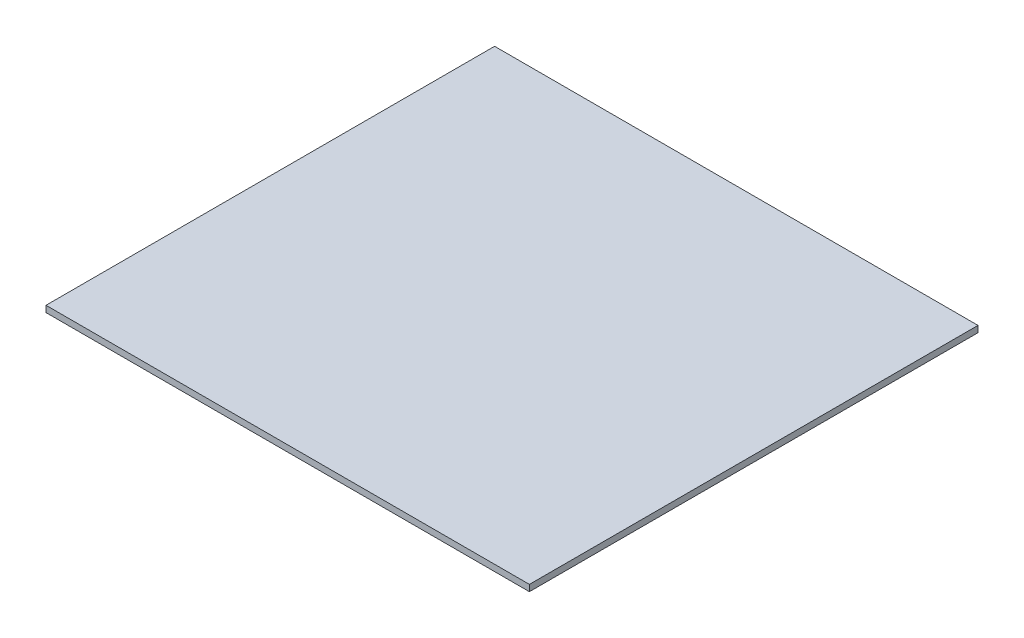
SolidWorks part; units mm, degrees
ref_plane "Front Plane" through (0, 0, 0) normal (0, 0, 1) x (1, 0, 0)
ref_plane "Top Plane" through (0, 0, 0) normal (0, 1, 0) x (1, 0, 0)
ref_plane "Right Plane" through (0, 0, 0) normal (1, 0, 0) x (0, 0, -1)
sketch "Sketch2" plane through (0, 0, 0) normal (0, 0, 1) x (1, 0, 0)
  line L0 (0, 25) -> (-380, 25)
  line L1 (-380, 25) -> (-380, 15)
  line L2 (-380, 15) -> (-225, 15)
  line L3 (-225, 15) -> (-225, 0)
  line L4 (-225, 0) -> (0, 0)
  line L5 (0, 25) -> (0, 0)
  dimension "D1" = 225
  dimension "D2" = 380
  dimension "D3" = 25
  dimension "D4" = 10
extrude "Boss-Extrude1" add sketch "Sketch2" along normal mid plane 605.25
mirror "Mirror1" about plane through (0, 25, 302.625) normal (-1, 0, 0) of "Boss-Extrude1"
sketch "Sketch3" plane through (0, 0, 302.625) normal (0, 0, 1) x (1, 0, 0)
  line L1 (-380, 25) -> (380, 25)
  line L2 (-380, 25) -> (-380, 15)
  line L3 (-380, 15) -> (380, 15)
  line L4 (380, 25) -> (380, 15)
  line L5 (-380, 25) -> (-380, 15) construction
  line L6 (380, 25) -> (380, 15) construction
  line L7 (380, 25) -> (-380, 25) construction
extrude "Boss-Extrude2" add sketch "Sketch3" along normal blind 50
sketch "Sketch4" plane through (0, 0, -302.625) normal (0, 0, -1) x (-1, 0, 0)
  line L0 (-380, 25) -> (-380, 15) construction
  line L1 (-380, 25) -> (380, 25)
  line L2 (-380, 25) -> (-380, 15)
  line L3 (-380, 15) -> (380, 15)
  line L4 (380, 25) -> (380, 15)
  line L5 (-380, 15) -> (-225, 15) construction
  line L6 (380, 25) -> (380, 15) construction
  line L7 (-380, 25) -> (380, 25) construction
extrude "Boss-Extrude3" add sketch "Sketch4" along normal blind 50
